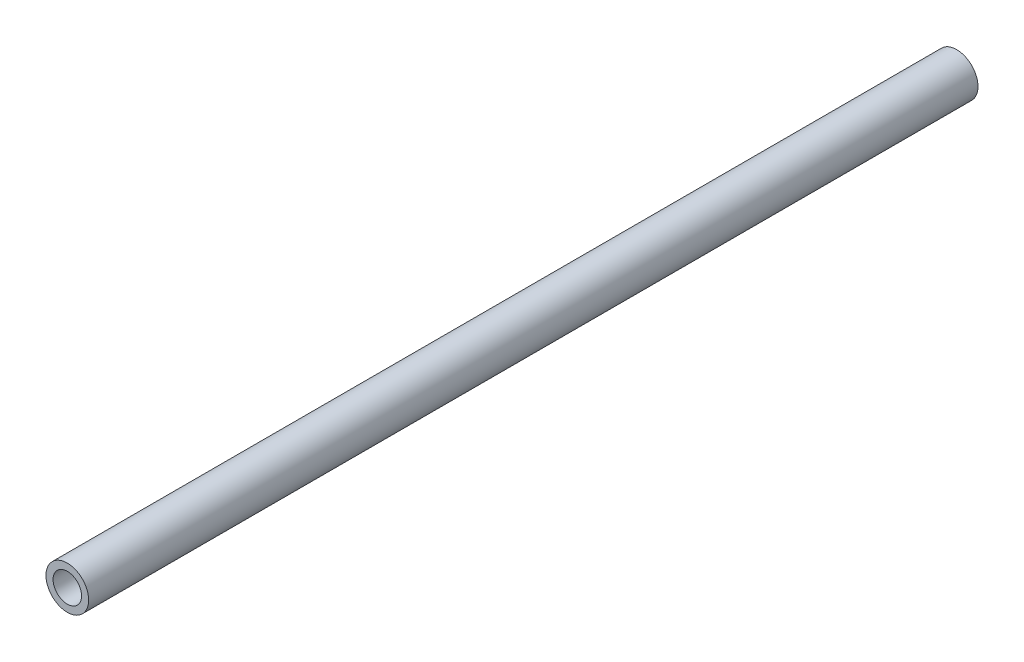
SolidWorks part; units mm, degrees
material "PVC Rigid"
ref_plane "Front Plane" through (0, 0, 0) normal (0, 0, 1) x (1, 0, 0)
ref_plane "Top Plane" through (0, 0, 0) normal (0, 1, 0) x (1, 0, 0)
ref_plane "Right Plane" through (0, 0, 0) normal (1, 0, 0) x (0, 0, -1)
sketch "Sketch1" plane through (0, 0, 0) normal (0, 0, 1) x (1, 0, 0)
  circle A0 centre (0, 0) radius 7.62
  circle A2 centre (0, 0) radius 5.08
  dimension "D1" = 15.24
  dimension "D2" = 10.16
extrude "Boss-Extrude1" add sketch "Sketch1" along normal blind 317.5
